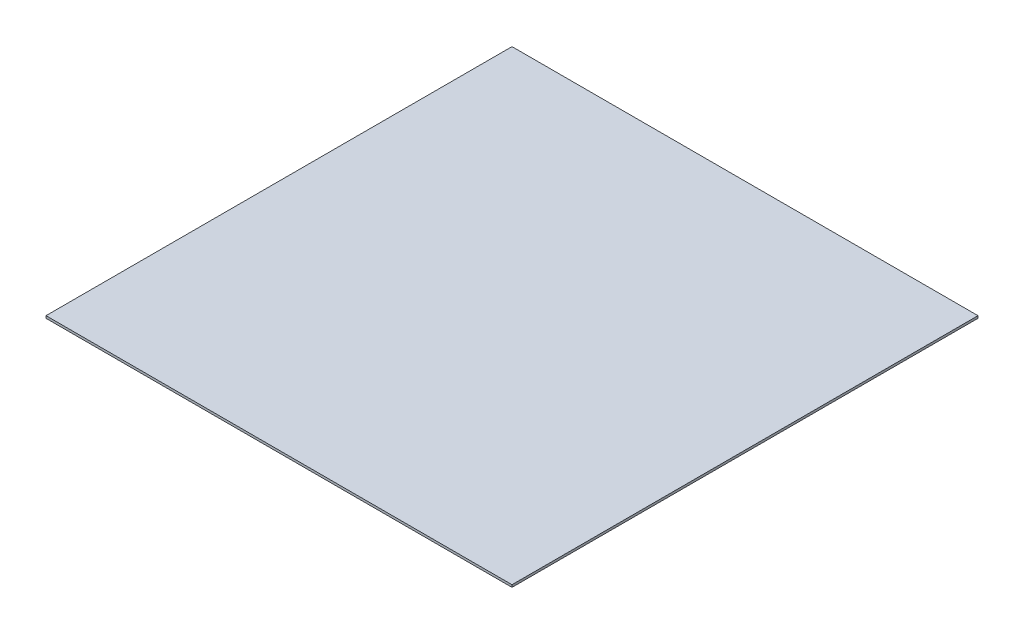
SolidWorks part; units mm, degrees
ref_plane "Front Plane" through (0, 0, 0) normal (0, 0, 1) x (1, 0, 0)
ref_plane "Top Plane" through (0, 0, 0) normal (0, 1, 0) x (1, 0, 0)
ref_plane "Right Plane" through (0, 0, 0) normal (1, 0, 0) x (0, 0, -1)
sketch "Sketch1" plane through (0, 0, 0) normal (0, 1, 0) x (1, 0, 0)
  line L1 (-48.6082, 2046.4521) -> (1951.3918, 2046.4521)
  line L2 (-48.6082, 2046.4521) -> (-48.6082, 46.4521)
  line L3 (-48.6082, 46.4521) -> (1951.3918, 46.4521)
  line L4 (1951.3918, 2046.4521) -> (1951.3918, 46.4521)
  dimension "D1" = 2000
  dimension "D2" = 2000
extrude "Boss-Extrude1" add sketch "Sketch1" along normal blind 10
